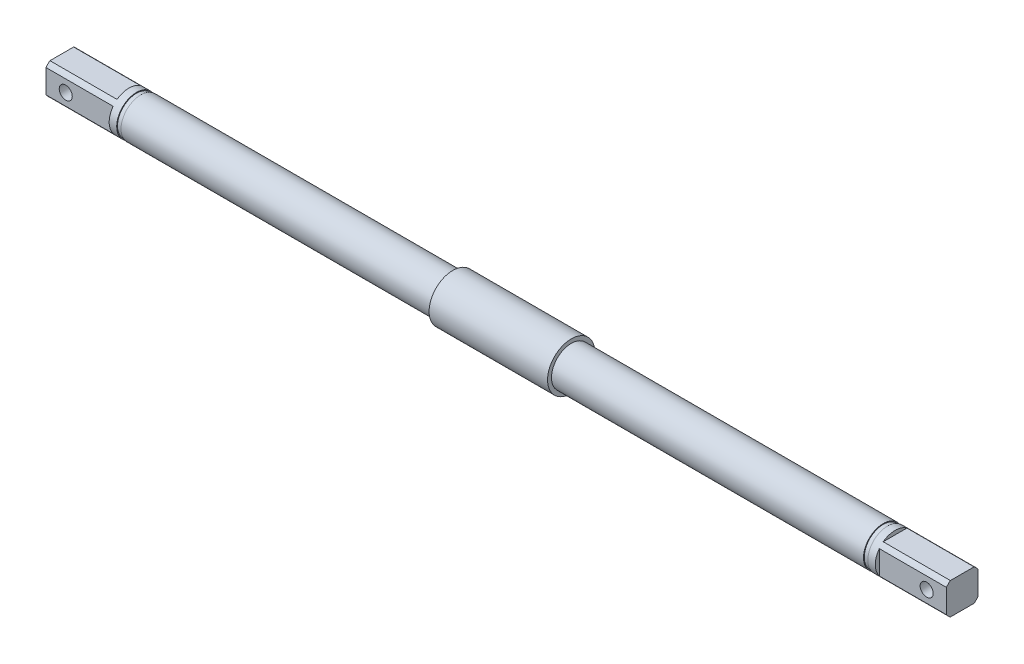
SolidWorks part; units mm, degrees
material "304"
ref_plane "前视基准面" through (0, 0, 0) normal (0, 0, 1) x (1, 0, 0)
ref_plane "上视基准面" through (0, 0, 0) normal (0, 1, 0) x (1, 0, 0)
ref_plane "右视基准面" through (0, 0, 0) normal (1, 0, 0) x (0, 0, -1)
sketch "草图1" plane through (0, 0, 0) normal (0, 0, 1) x (1, 0, 0)
  line L0 (-177.8106, 0) -> (177.8106, 0) construction
  line L1 (114, 0) -> (114, 5)
  line L2 (-114, 5) -> (-114, 0)
  line L3 (-95.1, 5) -> (-95.1, 4.8)
  line L4 (-95.1, 4.8) -> (-94, 4.8)
  line L5 (-15, 5) -> (-15, 6)
  line L6 (-15, 6) -> (15, 6)
  line L7 (15, 6) -> (15, 5)
  line L8 (-94, 4.8) -> (-94, 5)
  line L9 (-95.1, 5) -> (-114, 5)
  line L10 (15, 5) -> (94, 5)
  line L11 (95.1, 5) -> (114, 5)
  line L13 (94, 5) -> (94, 4.8)
  line L14 (0, 0) -> (0, 12) construction
  line L15 (-114, 0) -> (114, 0)
  line L16 (-15, 5) -> (-94, 5)
  line L17 (94, 4.8) -> (95.1, 4.8)
  line L18 (95.1, 5) -> (95.1, 4.8)
  point P19 (0, 6)
  dimension "D2" = 99
  dimension "D3" = 10
  dimension "D4" = 1.1
  dimension "D5" = 30
  dimension "D6" = 99
  dimension "D7" = 10
  dimension "D8" = 9.6
  dimension "D9" = 18.9
  dimension "D10" = 1.1
  dimension "D11" = 18.9
  dimension "D12" = 12
  dimension "D13" = 9.6
revolve "旋转1" add sketch "草图1" angle 360 about L15
sketch "草图2" plane through (114, 0, 0) normal (1, 0, 0) x (0, 0, -1)
  line L1 (-4, 4) -> (4, 4)
  line L2 (-4, 4) -> (-4, -4)
  line L3 (-4, -4) -> (4, -4)
  line L4 (4, 4) -> (4, -4)
  line L5 (-4, 4) -> (4, -4) construction
  line L6 (-4, -4) -> (4, 4) construction
  point P0 (0, 0)
  dimension "D1" = 8
  dimension "D2" = 8
extrude "切除-拉伸1" cut sketch "草图2" against normal blind 17 flip side to cut
mirror "镜向2" about plane through (0, 0, 0) normal (1, 0, 0) of "切除-拉伸1"
hole_wizard "M4 螺纹孔1" positions "草图4" profile "草图3" tap size "M4" standard "GB" end condition through all
sketch "草图4" plane through (0, 0, 4) normal (0, 0, 1) x (1, 0, 0)
  line L0 (114, 3) -> (114, -3) construction
  line L1 (-114, -3) -> (-114, 3) construction
  point P0 (109, 0)
  point P5 (-109, 0)
  point P8 (-114, 0)
  dimension "D1" = 5
  dimension "D2" = 5
sketch "草图3" plane through (109, 0, 4) normal (1, 0, 0) x (0, -1, 0)
  line L0 (0, 0) -> (0, 10)
  line L1 (0, 10) -> (1.65, 10)
  line L2 (1.65, 10) -> (1.65, 0)
  line L5 (1.65, 0) -> (0, 0)
  line L11 (0, -6.35) -> (0, 107.95) construction
  dimension "通孔螺纹孔钻头直径" = 3.3
  dimension "通孔螺纹孔钻头深度" = 10
cosmetic thread "孔螺蚊线1" parameters "D2"=4
cosmetic thread "孔螺蚊线2" parameters "D2"=4
